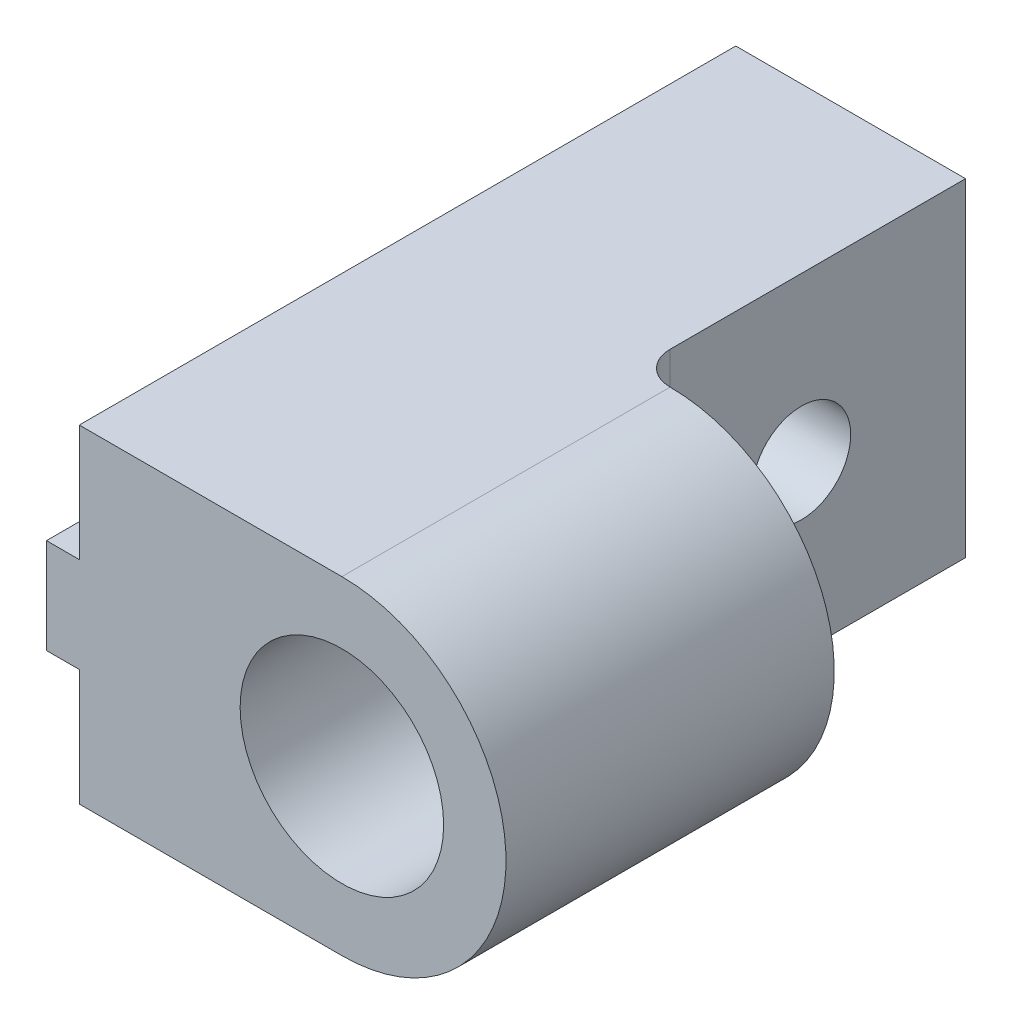
SolidWorks part; units mm, degrees
ref_plane "Front Plane" through (0, 0, 0) normal (0, 0, 1) x (1, 0, 0)
ref_plane "Top Plane" through (0, 0, 0) normal (0, 1, 0) x (1, 0, 0)
ref_plane "Right Plane" through (0, 0, 0) normal (1, 0, 0) x (0, 0, -1)
sketch "Sketch1" plane through (0, 0, 0) normal (0, 0, 1) x (1, 0, 0)
  line L0 (-8, 5) -> (-8, 1.45)
  line L1 (-8, 1.45) -> (-9, 1.45)
  line L2 (-9, 1.45) -> (-9, -1.45)
  line L3 (-9, -1.45) -> (-8, -1.45)
  line L4 (-8, -1.45) -> (-8, -5)
  line L5 (-8, -5) -> (0, -5)
  line L6 (-8, 5) -> (0, 5)
  arc A0 (0, -5) -> (0, 5) centre (0, 0) ccw
  dimension "D1" = 10
  dimension "D2" = 2.9
  dimension "D3" = 1
  dimension "D4" = 8
extrude "Main" add sketch "Sketch1" along normal blind 20
ref_plane "Plane1" through (-1, 0, 0) normal (-1, 0, 0) x (0, 0, 1)
sketch "Sketch2" plane through (0, 0, 20) normal (0, 0, 1) x (1, 0, 0)
  circle A0 centre (0, 0) radius 3.1
  dimension "D1" = 6.2
extrude "ShaftHole" cut sketch "Sketch2" against normal blind 5
sketch "Sketch3" plane through (-1, 0, 0) normal (1, 0, 0) x (0, 0, -1)
  line L0 (-20, 5) -> (0, 5) construction
  line L1 (-10, 5) -> (0, 5)
  line L2 (-10, 5) -> (-10, -5)
  line L3 (-10, -5) -> (0, -5)
  line L4 (0, 5) -> (0, -5)
  line L5 (-20, -5) -> (0, -5) construction
  line L6 (0, -5) -> (0, 5) construction
  dimension "D1" = 10
extrude "MakerBeamRectangularHole" cut sketch "Sketch3" along normal through all
sketch "Sketch4" plane through (-1, 0, 0) normal (1, 0, 0) x (0, 0, -1)
  line L0 (0, -5) -> (0, 5) construction
  circle A0 centre (-5, 0) radius 1.5
  dimension "D1" = 3
  dimension "D2" = 5
extrude "MakerBeamHole" cut sketch "Sketch4" against normal through all
fillet "Fillet1" radius 1 1 edges at (-1, 0, 10)
